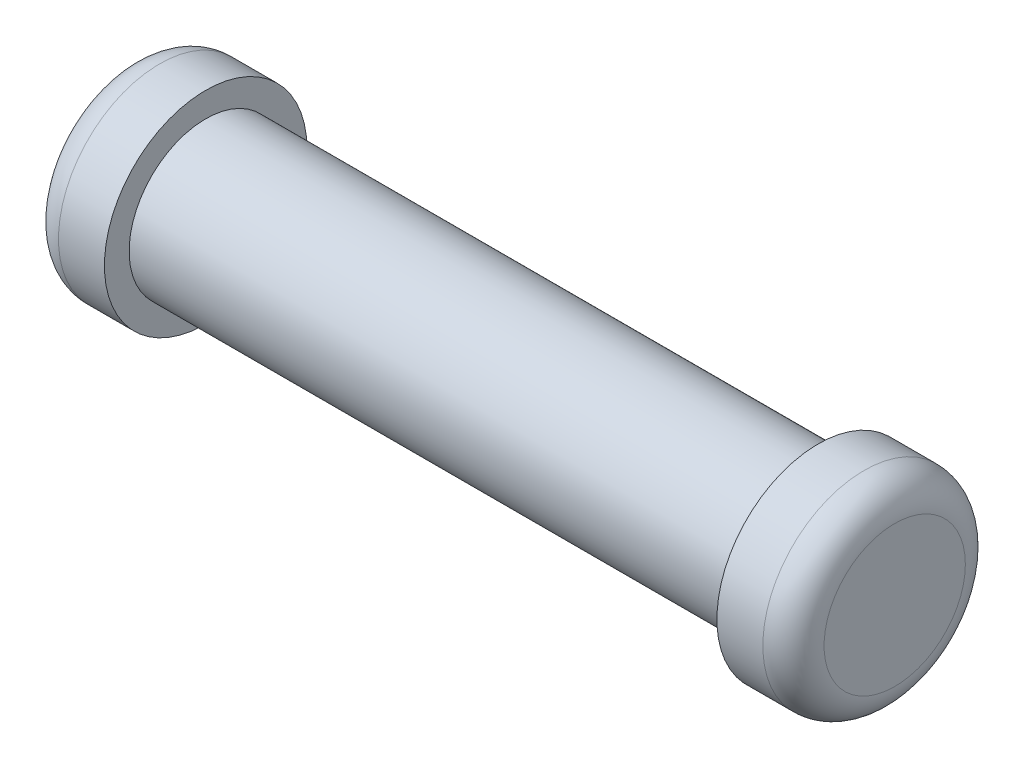
SolidWorks part; units mm, degrees
ref_plane "Front Plane" through (0, 0, 0) normal (0, 0, 1) x (1, 0, 0)
ref_plane "Top Plane" through (0, 0, 0) normal (0, 1, 0) x (1, 0, 0)
ref_plane "Right Plane" through (0, 0, 0) normal (1, 0, 0) x (0, 0, -1)
sketch "Sketch1" plane through (0, 0, 0) normal (0, 1, 0) x (1, 0, 0)
  line L0 (-100.7806, -25.4) -> (102.4194, -25.4)
  line L1 (102.4194, -25.4) -> (102.4194, -33.5935)
  line L2 (102.4194, -33.5935) -> (117.6594, -33.5935)
  line L3 (127.8194, -23.4335) -> (127.8194, 0)
  line L4 (127.8194, 0) -> (-126.1806, 0)
  line L5 (-126.1806, 0) -> (-126.1806, -23.4335)
  line L6 (-116.0206, -33.5935) -> (-100.7806, -33.5935)
  line L7 (-100.7806, -33.5935) -> (-100.7806, -25.4)
  arc A0 (-126.1806, -23.4335) -> (-116.0206, -33.5935) centre (-116.0206, -23.4335) ccw
  arc A1 (127.8194, -23.4335) -> (117.6594, -33.5935) centre (117.6594, -23.4335) cw
  point P11 (-126.1806, -33.5935)
  point P14 (127.8194, -33.5935)
  dimension "D6" = 10.16
  dimension "D7" = 10.16
  dimension "D1" = 25.4
  dimension "D2" = 33.5935
  dimension "D3" = 254
  dimension "D4" = 25.4
  dimension "D5" = 25.4
revolve "Revolve1" add sketch "Sketch1" angle 360 about L4
